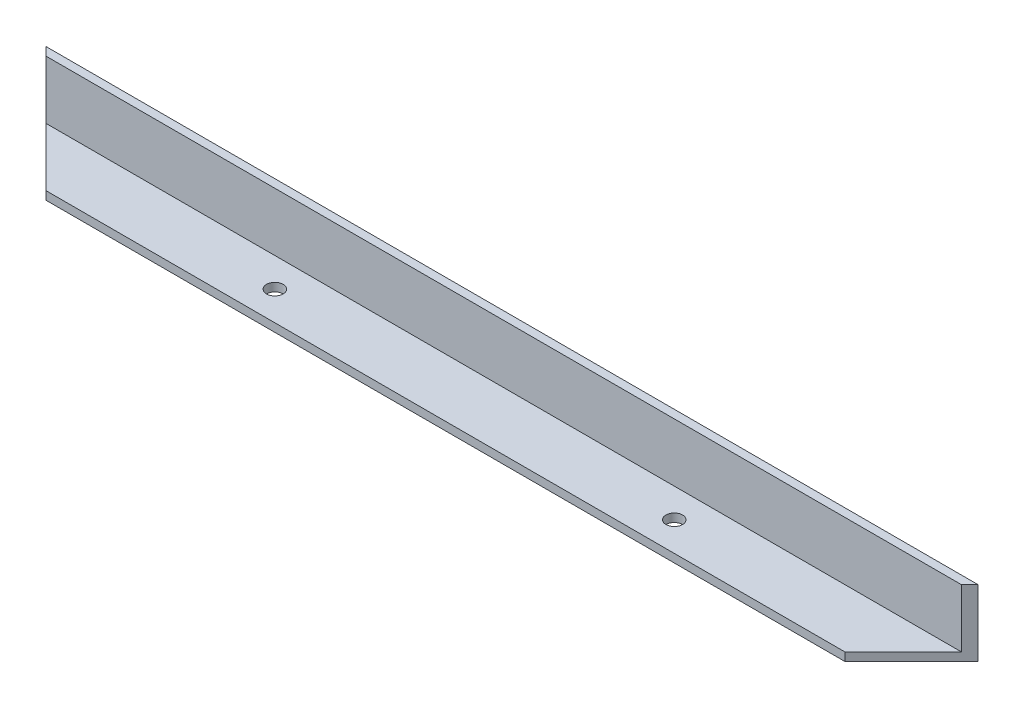
SolidWorks part; units mm, degrees
material "6063-T1"
ref_plane "Front Plane" through (0, 0, 0) normal (0, 0, 1) x (1, 0, 0)
ref_plane "Top Plane" through (0, 0, 0) normal (0, 1, 0) x (1, 0, 0)
ref_plane "Right Plane" through (0, 0, 0) normal (1, 0, 0) x (0, 0, -1)
sketch "Sketch2" plane through (0, 0, 0) normal (0, 1, 0) x (1, 0, 0)
  line L1 (0, 0) -> (-355.6, 0)
  line L2 (0, 0) -> (0, -25.4)
  line L3 (0, -25.4) -> (-355.6, -25.4)
  line L4 (-355.6, 0) -> (-355.6, -25.4)
  dimension "D1" = 355.6
  dimension "D2" = 25.4
extrude "Boss-Extrude1" add sketch "Sketch2" along normal blind 3.175
sketch "Sketch3" plane through (0, 3.175, 0) normal (0, 1, 0) x (1, 0, 0)
  line L1 (-355.6, 0) -> (0, 0)
  line L2 (-355.6, 0) -> (-355.6, -3.175)
  line L3 (-355.6, -3.175) -> (0, -3.175)
  line L4 (0, 0) -> (0, -3.175)
  dimension "D1" = 3.175
  dimension "D2" = 355.6
extrude "Boss-Extrude2" add sketch "Sketch3" along normal blind 22.225
sketch "Sketch6" plane through (0, 25.4, 0) normal (0, 1, 0) x (1, 0, 0)
  line L0 (-355.6, 0) -> (-314.4657, -41.1343)
  line L1 (-314.4657, -41.1343) -> (-387.8361, -49.3325)
  line L2 (-387.8361, -49.3325) -> (-355.6, 0)
  line L3 (0, 0) -> (-355.6, 0) construction
  line L4 (0, 0) -> (-41.6588, -41.6588)
  line L5 (-41.6588, -41.6588) -> (40.7558, -53.5203)
  line L6 (40.7558, -53.5203) -> (0, 0)
  dimension "D1" = 45
  dimension "D2" = 45
extrude "Cut-Extrude3" cut sketch "Sketch6" against normal up to surface (25.4 mm away) up to face at (-177.8, 0, 12.7)
sketch "Sketch7" plane through (0, 3.175, 0) normal (0, 1, 0) x (1, 0, 0)
  line L0 (-330.2, -25.4) -> (-25.4, -25.4) construction
  line L1 (-352.425, -3.175) -> (-3.175, -3.175) construction
  line L3 (-177.8, -25.4) -> (-177.8, -3.175) construction
  circle A0 centre (-101.6, -14.2875) radius 3.175
  circle A2 centre (-254, -14.2875) radius 3.175
  dimension "D1" = 6.35
  dimension "D5" = 152.4
  dimension "D4" = 76.2
  dimension "D2" = 22.225
  dimension "D3" = 11.1125
extrude "Cut-Extrude4" cut sketch "Sketch7" against normal up to surface (3.175 mm away) up to face at (-177.8, 0, 12.7)
